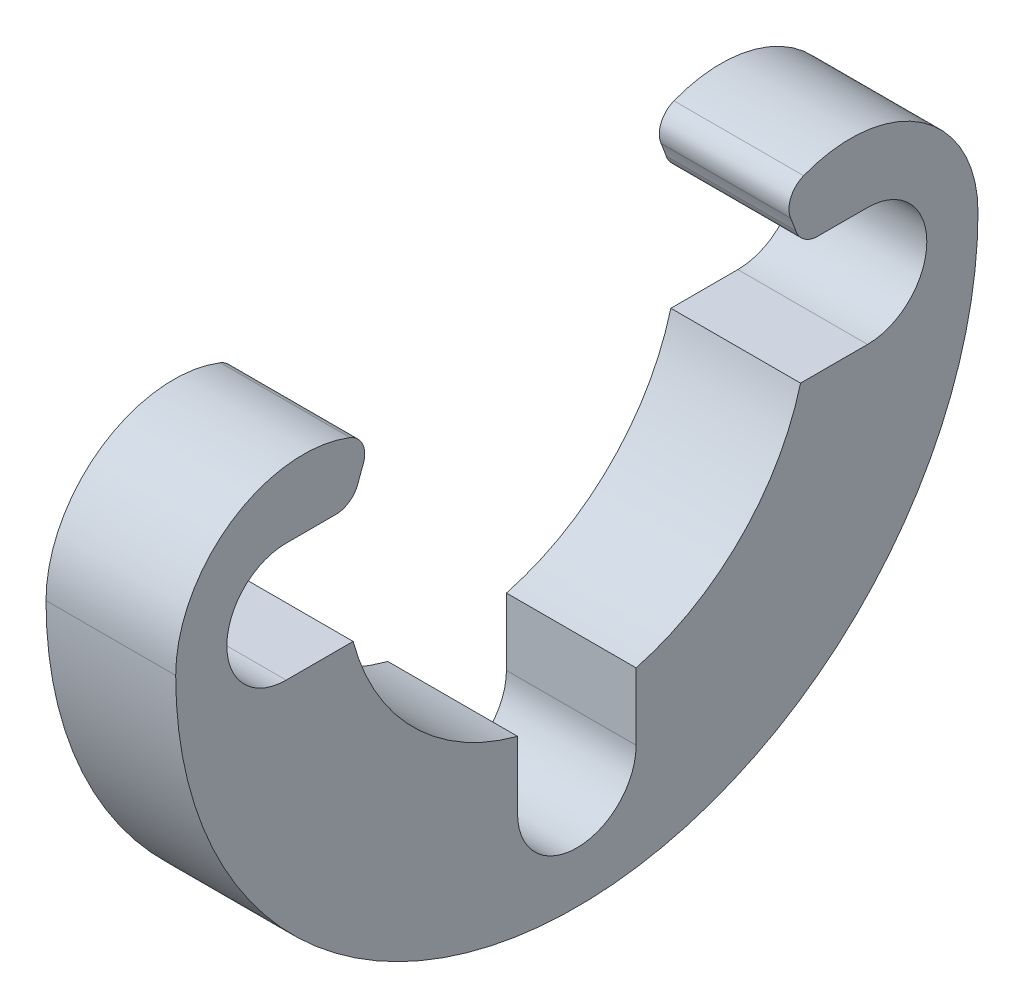
SolidWorks part; units mm, degrees
ref_plane "Front Plane" through (0, 0, 0) normal (0, 0, 1) x (1, 0, 0)
ref_plane "Top Plane" through (0, 0, 0) normal (0, 1, 0) x (1, 0, 0)
ref_plane "Right Plane" through (0, 0, 0) normal (1, 0, 0) x (0, 0, -1)
sketch "Sketch1" plane through (0, 0, 0) normal (0, 0, 1) x (1, 0, 0)
  line L0 (0, 0) -> (-15.1384, 0) construction
  line L2 (-15.1384, 5) -> (-5.1384, 5)
  line L3 (-5.1384, 5) -> (-5.1384, 11)
  line L9 (-5.1384, 11) -> (-1.5824, 11)
  line L10 (-1.5824, 11) -> (-1.5824, 5.08)
  line L11 (-1.5824, 5.08) -> (0, 5.08)
  line L12 (-15.1384, 5) -> (-15.1384, 4)
  line L13 (-15.1384, 4) -> (0, 4)
  line L14 (0, 4) -> (0, 5.08)
  dimension "D1" = 5
  dimension "D2" = 5.08
  dimension "D3" = 10
  dimension "D4" = 22
  dimension "D5" = 8
  dimension "D6" = 3.556
  dimension "D7" = 15.1384
revolve "Revolve1" add sketch "Sketch1" angle 360 about L0
sketch "Sketch2" plane through (-1.5824, 0, 0) normal (1, 0, 0) x (0, 0, -1)
  circle A0 centre (0, 7.971) radius 1.6256
  circle A1 centre (0, 0) radius 11 construction
  dimension "D1" = 3.2512
  dimension "D2" = 1.4034
extrude "Cut-Extrude1" cut sketch "Sketch2" against normal up to surface (3.556 mm away) up to face at (-5.1384, 5, 0)
pattern_circular "CirPattern1" count 4 over 360 about axis through (0, 0, 0) along (1, 0, 0) of "Cut-Extrude1"
sketch "Sketch3" plane through (-1.5824, 0, 0) normal (1, 0, 0) x (0, 0, -1)
  line L0 (-4.216, 10.16) -> (4.216, 10.16)
  circle A0 centre (0, 0) radius 11 construction
  arc A1 (4.216, 10.16) -> (-4.216, 10.16) centre (0, 0) ccw
  point P0 (0, 10.16)
  dimension "D1" = 10.16
extrude "Cut-Extrude2" cut sketch "Sketch3" against normal up to surface (3.556 mm away) up to face at (-5.1384, -1.6256, -7.971)
sketch "Sketch4" plane through (-15.1384, 0, 0) normal (-1, 0, 0) x (0, 0, 1)
  circle A1 centre (0, 0) radius 5
  circle A2 centre (0, 0) radius 5
  dimension "D1" = 0
extrude "Cut-Extrude3" cut sketch "Sketch4" against normal up to surface (10 mm away) up to face at (-5.1384, -0.42, 0)
sketch "Sketch5" plane through (-5.1384, 0, 0) normal (-1, 0, 0) x (0, 0, 1)
  arc A0 (-4, 0) -> (-11, 0) centre (-7.5, 0) ccw
  circle A1 centre (0, 0) radius 4 construction
  arc A2 (-4.216, 10.16) -> (4.216, 10.16) centre (0, 0) ccw construction
  arc A3 (4, 0) -> (11, 0) centre (7.5, 0) cw
  arc A4 (-11, 0) -> (11, 0) centre (0, 0) cw
  arc A5 (-4, 0) -> (4, 0) centre (0, 0) cw
extrude "Cut-Extrude4" cut sketch "Sketch5" against normal up to surface (3.556 mm away) up to face at (-1.5824, -0.42, 0)
sketch "Sketch6" plane through (0, 0, 0) normal (1, 0, 0) x (0, 0, -1)
  circle A1 centre (0, 0) radius 5.08
  circle A2 centre (0, 0) radius 5.08
  dimension "D1" = 0
extrude "Cut-Extrude5" cut sketch "Sketch6" against normal up to surface (1.5824 mm away) up to face at (-1.5824, 0, 9.5967)
sketch "Sketch7" plane through (-5.1384, 0, 0) normal (-1, 0, 0) x (0, 0, 1)
  line L0 (-7.971, 1.6256) -> (-6.1337, 1.6256)
  line L1 (-7.971, -1.6256) -> (-6.1337, -1.6256)
  line L2 (-1.6256, -7.9711) -> (-1.6256, -6.1337)
  line L3 (1.6256, -7.9711) -> (1.6256, -6.1337)
  line L4 (7.971, 1.6256) -> (6.1337, 1.6256)
  line L5 (7.971, -1.6256) -> (6.1337, -1.6256)
  arc A0 (6.1337, 1.6256) -> (-6.1337, 1.6256) centre (0, 0) ccw
  circle A1 centre (-7.971, 0) radius 1.6256 construction
  circle A2 centre (0, -7.9711) radius 1.6256 construction
  circle A3 centre (7.971, 0) radius 1.6256 construction
  arc A4 (-6.1337, -1.6256) -> (-1.6256, -6.1337) centre (0, 0) ccw
  arc A5 (1.6256, -6.1337) -> (6.1337, -1.6256) centre (0, 0) ccw
  arc A6 (7.971, 1.6256) -> (7.971, -1.6256) centre (7.971, 0) ccw
  arc A7 (-1.6256, -7.9711) -> (1.6256, -7.9711) centre (0, -7.9711) cw
  arc A8 (-7.971, 1.6256) -> (-7.971, -1.6256) centre (-7.971, 0) cw
extrude "Cut-Extrude6" cut sketch "Sketch7" against normal through all
fillet "Fillet1" radius 0.635 4 edges at (-3.3604, 2.9507, -5.6176) (-3.3604, 1.6256, -6.1337) (-3.3604, 2.9507, 5.6176) (-3.3604, 1.6256, 6.1337)
